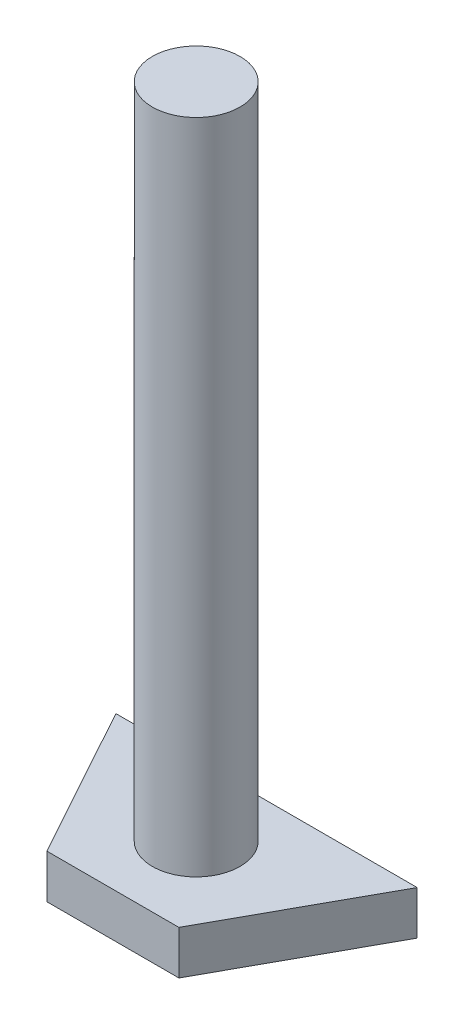
SolidWorks part; units mm, degrees
ref_plane "Front Plane" through (0, 0, 0) normal (0, 0, 1) x (1, 0, 0)
ref_plane "Top Plane" through (0, 0, 0) normal (0, 1, 0) x (1, 0, 0)
ref_plane "Right Plane" through (0, 0, 0) normal (1, 0, 0) x (0, 0, -1)
sketch "Sketch1" plane through (0, 0, 0) normal (0, 1, 0) x (1, 0, 0)
  circle A0 centre (76.5581, 38.3937) radius 2
extrude "Boss-Extrude1" add sketch "Sketch1" along normal blind 30
sketch "Sketch2" plane through (0, 0, 0) normal (0, -1, 0) x (1, 0, 0)
  line L1 (79.5699, -34.5947) -> (73.5463, -34.5947)
  line L2 (73.5463, -34.5947) -> (69.6872, -41.6024)
  line L3 (69.6872, -41.6024) -> (83.429, -41.6024)
  line L4 (79.5699, -34.5947) -> (83.429, -41.6024)
  point P9 (76.5581, -41.6024)
  point P10 (76.5581, -34.5947)
extrude "Boss-Extrude2" add sketch "Sketch2" along normal blind 2
